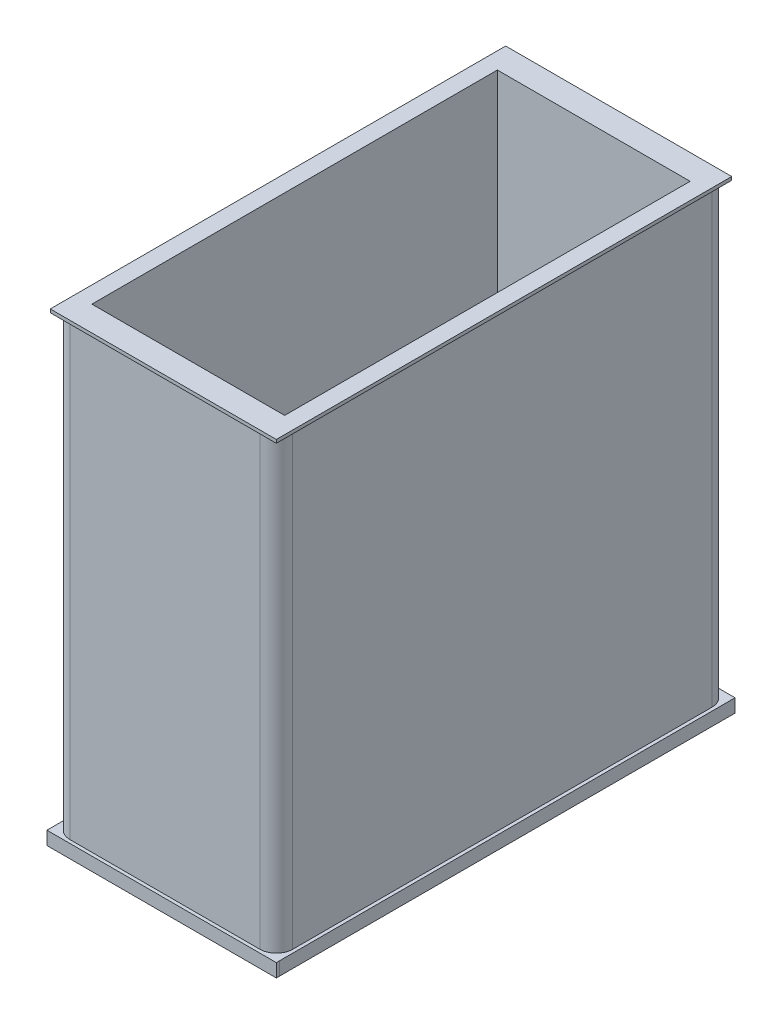
SolidWorks part; units mm, degrees
other "Camera1"
ref_plane "Front Plane" through (0, 0, 0) normal (0, 0, 1) x (1, 0, 0)
ref_plane "Top Plane" through (0, 0, 0) normal (0, 1, 0) x (1, 0, 0)
ref_plane "Right Plane" through (0, 0, 0) normal (1, 0, 0) x (0, 0, -1)
sketch "Sketch1" plane through (0, 0, 0) normal (0, 1, 0) x (1, 0, 0)
  line L2 (-66.3338, 134.988) -> (103.5922, 134.988)
  line L3 (-66.3338, 134.988) -> (-66.3338, -209.944)
  line L4 (-66.3338, -209.944) -> (103.5922, -209.944)
  line L5 (103.5922, 134.988) -> (103.5922, -209.944)
  dimension "D1" = 344.932
  dimension "D2" = 169.926
extrude "Boss-Extrude1" add sketch "Sketch1" along normal blind 379.984
sketch "Sketch7" plane through (-66.3338, 0, 0) normal (-1, 0, 0) x (0, 0, 1)
  line L0 (-134.988, 0) -> (209.944, 0)
  line L1 (-134.988, 0) -> (-134.988, 10.16)
  line L2 (209.944, 0) -> (209.944, 10.16)
  line L3 (-134.988, 10.16) -> (209.944, 10.16)
  dimension "D1" = 10.16
extrude "Boss-Extrude4" add sketch "Sketch7" along normal blind 2.54
sketch "Sketch8" plane through (103.5922, 0, 0) normal (1, 0, 0) x (0, 0, -1)
  line L0 (-209.944, 0) -> (134.988, 0)
  line L1 (-209.944, 0) -> (-209.944, 10.16)
  line L2 (134.988, 0) -> (134.988, 10.16)
  line L3 (-209.944, 10.16) -> (134.988, 10.16)
  dimension "D1" = 10.16
extrude "Boss-Extrude5" add sketch "Sketch8" along normal blind 2.54
sketch "Sketch9" plane through (0, 0, -134.988) normal (0, 0, -1) x (-1, 0, 0)
  line L0 (-106.1322, 0) -> (68.8738, 0)
  line L1 (-106.1322, 0) -> (-106.1322, 10.16)
  line L2 (68.8738, 0) -> (68.8738, 10.16)
  line L3 (-106.1322, 10.16) -> (68.8738, 10.16)
extrude "Boss-Extrude6" add sketch "Sketch9" along normal blind 2.54
sketch "Sketch13" plane through (103.5922, 0, 0) normal (1, 0, 0) x (0, 0, -1)
  line L0 (-209.944, 354.584) -> (134.988, 354.584)
  line L1 (-209.944, 354.584) -> (-209.944, 352.044)
  line L2 (134.988, 354.584) -> (134.988, 352.044)
  line L3 (-209.944, 352.044) -> (134.988, 352.044)
  line L4 (-209.944, 379.984) -> (-209.944, 10.16) construction
  line L5 (134.988, 379.984) -> (134.988, 10.16) construction
  line L6 (-209.944, 379.984) -> (134.988, 379.984) construction
  dimension "D1" = 2.54
  dimension "D2" = 25.4
extrude "Boss-Extrude9" add sketch "Sketch13" along normal blind 1.27
sketch "Sketch14" plane through (0, 0, -134.988) normal (0, 0, -1) x (-1, 0, 0)
  line L6 (-104.8622, 352.044) -> (66.3338, 352.044)
  line L7 (-104.8622, 352.044) -> (-104.8622, 354.584)
  line L8 (66.3338, 352.044) -> (66.3338, 354.584)
  line L9 (-104.8622, 354.584) -> (66.3338, 354.584)
  line L10 (66.3338, 379.984) -> (66.3338, 10.16) construction
  dimension "D1" = 2.54
extrude "Boss-Extrude10" add sketch "Sketch14" along normal blind 1.27
sketch "Sketch15" plane through (-66.3338, 0, 0) normal (-1, 0, 0) x (0, 0, 1)
  line L0 (-136.258, 352.044) -> (209.944, 352.044)
  line L1 (-136.258, 352.044) -> (-136.258, 354.584)
  line L2 (209.944, 352.044) -> (209.944, 354.584)
  line L3 (-136.258, 354.584) -> (209.944, 354.584)
  line L4 (209.944, 379.984) -> (209.944, 10.16) construction
  dimension "D1" = 2.54
extrude "Boss-Extrude11" add sketch "Sketch15" along normal blind 1.27
sketch "Sketch16" plane through (0, 0, 209.944) normal (0, 0, 1) x (1, 0, 0)
  line L0 (-67.6038, 352.044) -> (104.8622, 352.044)
  line L1 (-67.6038, 352.044) -> (-67.6038, 354.584)
  line L2 (104.8622, 352.044) -> (104.8622, 354.584)
  line L3 (-67.6038, 354.584) -> (104.8622, 354.584)
  dimension "D1" = 2.54
extrude "Boss-Extrude12" add sketch "Sketch16" along normal blind 1.27
ref_plane "Plane3" through (0, 0, -134.988) normal (0, 0, -1) x (-1, 0, 0)
fillet "Fillet1" radius 12.54 12 edges at (103.5922, 379.984, 37.478) (18.6292, 379.984, -134.988) (-66.3338, 379.984, 37.478) (103.5922, 181.102, 209.944) (103.5922, 181.102, -134.988) (-66.3338, 181.102, -134.988) (-66.3338, 367.284, -134.988) (103.5922, 367.284, -134.988) (103.5922, 367.284, 209.944) (-66.3338, 367.284, 209.944) (-66.3338, 181.102, 209.944) (18.6292, 379.984, 209.944)
sketch "Sketch23" plane through (0, 0, 209.944) normal (0, 0, 1) x (1, 0, 0)
  line L0 (-68.8738, 10.16) -> (-68.8738, 0)
  line L1 (-68.8738, 10.16) -> (106.141, 10.16)
  line L2 (-68.8738, 0) -> (106.141, 0)
  line L3 (106.141, 10.16) -> (106.141, 0)
extrude "Boss-Extrude15" add sketch "Sketch23" along normal blind 2.54
sketch "Sketch25" plane through (0, 0, -134.988) normal (0, 0, -1) x (-1, 0, 0)
  line L1 (-103.5922, 354.584) -> (76.696, 354.584)
  line L2 (-103.5922, 354.584) -> (-103.5922, 383.24)
  line L3 (-103.5922, 383.24) -> (76.696, 383.24)
  line L4 (76.696, 354.584) -> (76.696, 383.24)
extrude "Cut-Extrude1" cut sketch "Sketch25" against normal blind 474.472
sketch "Sketch26" plane through (0, 354.584, 0) normal (0, 1, 0) x (1, 0, 0)
  line L0 (104.8622, -211.214) -> (-67.6038, -211.214) construction
  line L1 (-54.9038, 117.208) -> (92.1622, 117.208)
  line L2 (-54.9038, 117.208) -> (-54.9038, -192.164)
  line L3 (-54.9038, -192.164) -> (92.1622, -192.164)
  line L4 (92.1622, 117.208) -> (92.1622, -192.164)
  line L5 (-67.6038, 136.258) -> (104.8622, 136.258) construction
  line L6 (104.8622, 136.258) -> (104.8622, -211.214) construction
  line L7 (-67.6038, -211.214) -> (-67.6038, 136.258) construction
  dimension "D1" = 19.05
  dimension "D2" = 19.05
  dimension "D3" = 12.7
  dimension "D4" = 12.7
extrude "Cut-Extrude2" cut sketch "Sketch26" against normal blind 345.948
